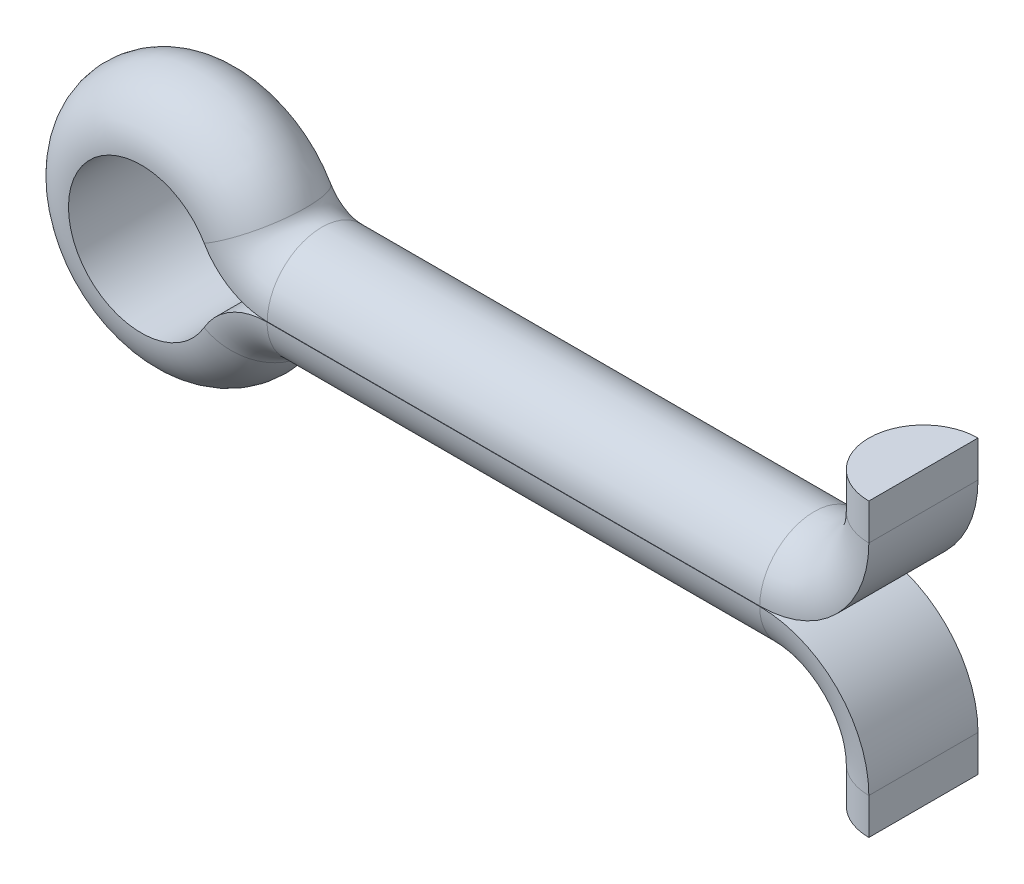
SolidWorks part; units mm, degrees
ref_plane "Front Plane" through (0, 0, 0) normal (0, 0, 1) x (1, 0, 0)
ref_plane "Top Plane" through (0, 0, 0) normal (0, 1, 0) x (1, 0, 0)
ref_plane "Right Plane" through (0, 0, 0) normal (1, 0, 0) x (0, 0, -1)
sketch "Sketch1" plane through (0, 0, 0) normal (0, 0, 1) x (1, 0, 0)
  line L0 (3.4641, 0) -> (17, 0)
  line L1 (20, 3) -> (20, 4)
  line L2 (3.4583, -0.01) -> (17, -0.01)
  line L3 (20, -3.01) -> (20, -4.01)
  arc A0 (1.7321, 1) -> (1.7292, -1.005) centre (0, 0) ccw
  arc A1 (3.4583, -0.01) -> (1.7292, -1.005) centre (3.4583, -2.01) ccw
  arc A2 (3.4641, 0) -> (1.7321, 1) centre (3.4641, 2) cw
  arc A3 (17, -0.01) -> (20, -3.01) centre (17, -3.01) cw
  arc A4 (17, 0) -> (20, 3) centre (17, 3) ccw
  point P12 (2, 0)
  point P15 (20, -0.01)
  point P18 (20, 0)
  dimension "D1" = 2
  dimension "D5" = 2
  dimension "D6" = 3
  dimension "D2" = 20
  dimension "D3" = 4
  dimension "D4" = 4
  dimension "D7" = 0.01
ref_plane "Plane1" through (20, 4, 0) normal (0, 1, 0) x (1, 0, 0)
sketch "Sketch3" plane through (20, 4, 0) normal (0, 1, 0) x (1, 0, 0)
  line L0 (0, 1.5) -> (0, -1.5)
  arc A0 (0, 1.5) -> (0, -1.5) centre (0, 0) ccw
  dimension "D1" = 3
sweep "Sweep1" add profiles "Sketch3" path "Sketch1"
